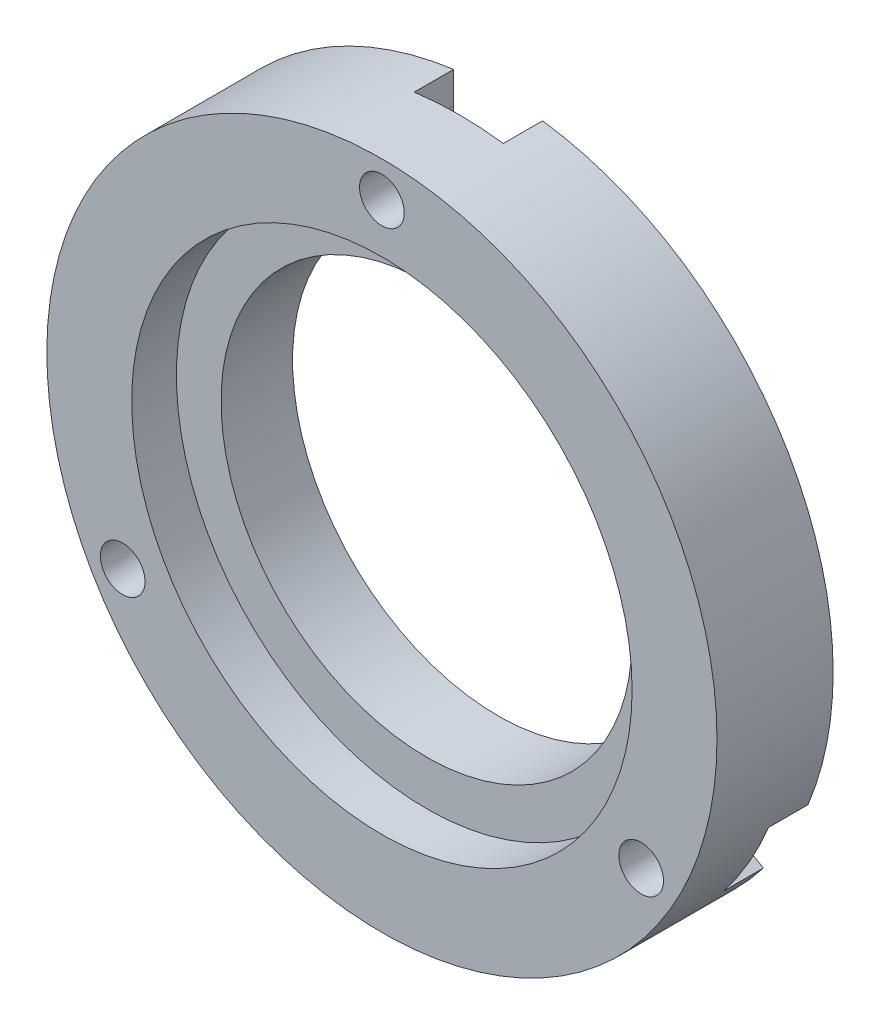
SolidWorks part; units mm, degrees
ref_plane "前视基准面" through (0, 0, 0) normal (0, 0, 1) x (1, 0, 0)
ref_plane "上视基准面" through (0, 0, 0) normal (0, 1, 0) x (1, 0, 0)
ref_plane "右视基准面" through (0, 0, 0) normal (1, 0, 0) x (0, 0, -1)
sketch "草图1" plane through (0, 0, 0) normal (0, 0, 1) x (1, 0, 0)
  circle A0 centre (0, 0) radius 18.75
  circle A17 centre (0, 0) radius 18.75
  circle A18 centre (14.5059, -8.375) radius 1.25
  circle A19 centre (-14.5059, -8.375) radius 1.25
  circle A20 centre (0, 16.75) radius 1.25
  circle A21 centre (0, 0) radius 11.5
  point P36 (0, 0)
extrude "凸台-拉伸1" add sketch "草图1" along normal blind 6.5 contours A0 A21 A20 A19 A18
sketch "草图2" plane through (0, 0, 6.5) normal (0, 0, 1) x (1, 0, 0)
  circle A0 centre (0, 0) radius 14
extrude "切除-拉伸1" cut sketch "草图2" against normal blind 2.5
sketch "草图3" plane through (0, 0, 0) normal (0, 0, -1) x (-1, 0, 0)
  arc A0 (16.9726, -7.9682) -> (15.387, -10.7146) centre (14.5059, -8.375) ccw
  circle A1 centre (0, 0) radius 18.75 construction
  arc A2 (15.387, -10.7146) -> (16.9726, -7.9682) centre (0, 0) ccw
  arc A3 (-15.387, -10.7146) -> (-16.9726, -7.9682) centre (-14.5059, -8.375) ccw
  arc A4 (-16.9726, -7.9682) -> (-15.387, -10.7146) centre (0, 0) ccw
  arc A5 (-1.5856, 18.6828) -> (1.5856, 18.6828) centre (0, 16.75) ccw
  arc A6 (1.5856, 18.6828) -> (-1.5856, 18.6828) centre (0, 0) ccw
  point P14 (0, 0)
  dimension "D1" = 3
extrude "切除-拉伸2" cut sketch "草图3" against normal blind 2.2
sketch "草图4" plane through (0, 0, 0) normal (0, 0, -1) x (-1, 0, 0)
  line L0 (-15.7217, -6.1905) -> (-17.339, -7.1359)
  line L1 (-14.8482, -11.4496) -> (-13.1991, -10.5062)
  line L2 (13.222, -10.5201) -> (14.8494, -11.4481)
  line L3 (2.4997, 16.7106) -> (2.4896, 18.584)
  line L4 (17.3397, -7.1341) -> (15.6982, -6.1776)
  line L5 (-2.4915, 18.5837) -> (-2.4991, 16.6838)
  arc A1 (15.387, -10.7146) -> (16.9726, -7.9682) centre (0, 0) ccw construction
  arc A2 (17.3409, -7.1314) -> (17.3072, -7.1152) centre (16.238, -9.375) ccw
  arc A3 (16.9726, -7.9682) -> (15.387, -10.7146) centre (14.5059, -8.375) ccw construction
  arc A4 (14.7991, -11.4194) -> (14.8464, -11.4519) centre (16.238, -9.375) ccw
  arc A5 (14.8464, -11.4519) -> (15.387, -10.7146) centre (0, 0) ccw
  arc A6 (-14.8464, -11.4519) -> (-14.8155, -11.4309) centre (-16.238, -9.375) ccw
  arc A7 (-17.289, -7.1067) -> (-17.3409, -7.1314) centre (-16.238, -9.375) ccw
  arc A8 (-17.3409, -7.1314) -> (-16.9726, -7.9682) centre (0, 0) ccw
  arc A9 (-15.387, -10.7146) -> (-13.1991, -10.5062) centre (-14.5059, -8.375) ccw
  arc A10 (-15.387, -10.7146) -> (-14.8464, -11.4519) centre (0, 0) ccw
  arc A11 (-2.4944, 18.5833) -> (-2.4917, 18.546) centre (0, 18.75) ccw
  arc A12 (16.9726, -7.9682) -> (15.387, -10.7146) centre (14.5059, -8.375) ccw construction
  arc A13 (16.9726, -7.9682) -> (15.6982, -6.1776) centre (14.5059, -8.375) ccw
  arc A14 (16.9726, -7.9682) -> (17.3409, -7.1314) centre (0, 0) ccw
  arc A15 (2.49, 18.5261) -> (2.4944, 18.5833) centre (0, 18.75) ccw
  arc A16 (2.4944, 18.5833) -> (1.5856, 18.6828) centre (0, 0) ccw
  arc A17 (-1.5856, 18.6828) -> (-2.4991, 16.6838) centre (0, 16.75) ccw
  arc A18 (-1.5856, 18.6828) -> (-2.4944, 18.5833) centre (0, 0) ccw
  arc A19 (13.222, -10.5201) -> (15.387, -10.7146) centre (14.5059, -8.375) ccw
  arc A20 (-15.7217, -6.1905) -> (-16.9726, -7.9682) centre (-14.5059, -8.375) ccw
  arc A21 (2.4997, 16.7106) -> (1.5856, 18.6828) centre (0, 16.75) ccw
  point P47 (0, 0)
  arc M20 (-15.387, -10.7146) -> (15.387, -10.7146) centre (0, 0) ccw
  arc M21 (15.387, -10.7146) -> (16.9726, -7.9682) centre (14.5059, -8.375) cw
  arc M22 (16.9726, -7.9682) -> (1.5856, 18.6828) centre (0, 0) ccw
  arc M23 (1.5856, 18.6828) -> (-1.5856, 18.6828) centre (0, 16.75) cw
  arc M24 (-1.5856, 18.6828) -> (-16.9726, -7.9682) centre (0, 0) ccw
  arc M25 (-16.9726, -7.9682) -> (-15.387, -10.7146) centre (-14.5059, -8.375) cw
extrude "切除-拉伸3" cut sketch "草图4" against normal blind 2.2 contours L1 M20 M25 | L0 M25 M24 | L2 M21 M20 | L4 M22 M21 | L5 M24 M23 | L3 M23 M22
